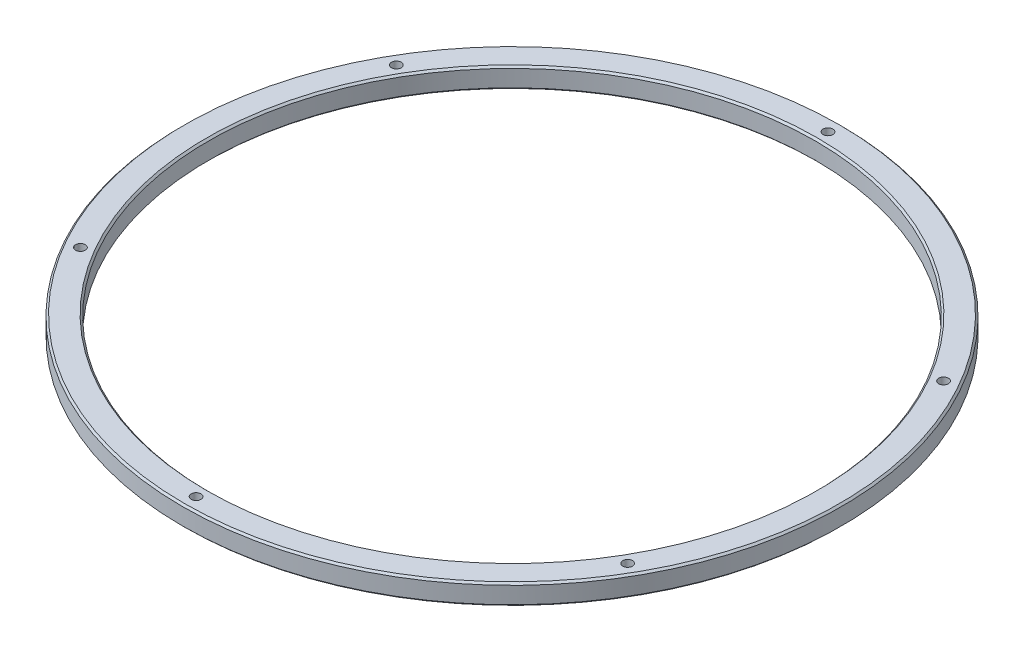
SolidWorks part; units mm, degrees
ref_plane "Front Plane" through (0, 0, 0) normal (0, 0, 1) x (1, 0, 0)
ref_plane "Top Plane" through (0, 0, 0) normal (0, 1, 0) x (1, 0, 0)
ref_plane "Right Plane" through (0, 0, 0) normal (1, 0, 0) x (0, 0, -1)
sketch "Sketch1" plane through (0, 0, 0) normal (0, 1, 0) x (1, 0, 0)
  circle A0 centre (0, 0) radius 161.157
  circle A1 centre (0, 0) radius 148.457
  circle A2 centre (0, 154.5) radius 2.3812
  circle A3 centre (0, 0) radius 154.5 construction
  circle A4 centre (133.8009, 77.25) radius 2.3813
  circle A5 centre (133.8009, -77.25) radius 2.3813
  circle A6 centre (0, -154.5) radius 2.3812
  circle A7 centre (-133.8009, -77.25) radius 2.3813
  circle A8 centre (-133.8009, 77.25) radius 2.3813
  dimension "D1" = 12.7
  dimension "D2" = 322.314
  dimension "D3" = 4.7625
  dimension "D4" = 309
  dimension "D6" = 60
  dimension "D7" = 60
  dimension "D5" = 6
extrude "Boss-Extrude1" add sketch "Sketch1" along normal blind 10
chamfer "Chamfer1" distance 0.889 angle 45 4 edges at (0, 10, 161.157) (0, 0, 148.457) (0, 10, 148.457) (0, 0, 161.157)
chamfer "Chamfer2" distance 2.54 angle 40 3 edges at (133.8009, 0, 79.6313) (-133.8009, 0, 79.6312) (0, 0, -152.1188)
